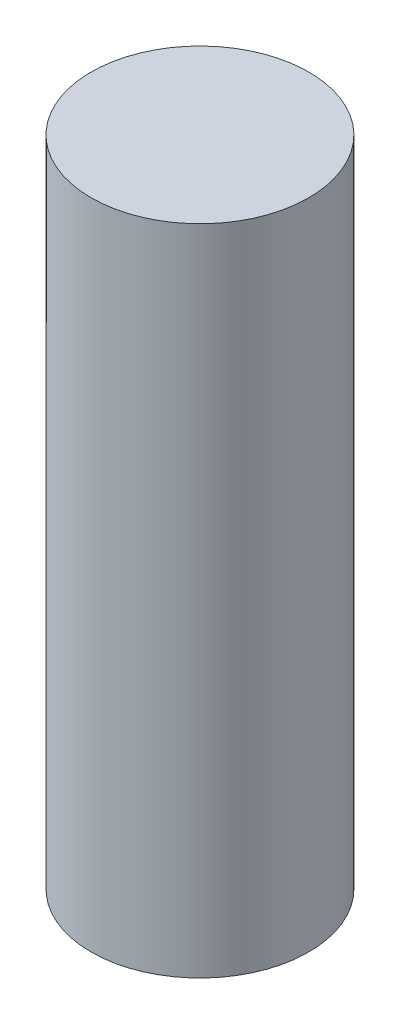
SolidWorks part; units mm, degrees
ref_plane "Front Plane" through (0, 0, 0) normal (0, 0, 1) x (1, 0, 0)
ref_plane "Top Plane" through (0, 0, 0) normal (0, 1, 0) x (1, 0, 0)
ref_plane "Right Plane" through (0, 0, 0) normal (1, 0, 0) x (0, 0, -1)
sketch "Sketch1" plane through (0, 0, 0) normal (0, 1, 0) x (1, 0, 0)
  circle A0 centre (0, 0) radius 1.25
  dimension "D1" = 2.5
extrude "Boss-Extrude1" add sketch "Sketch1" along normal blind 7.5
